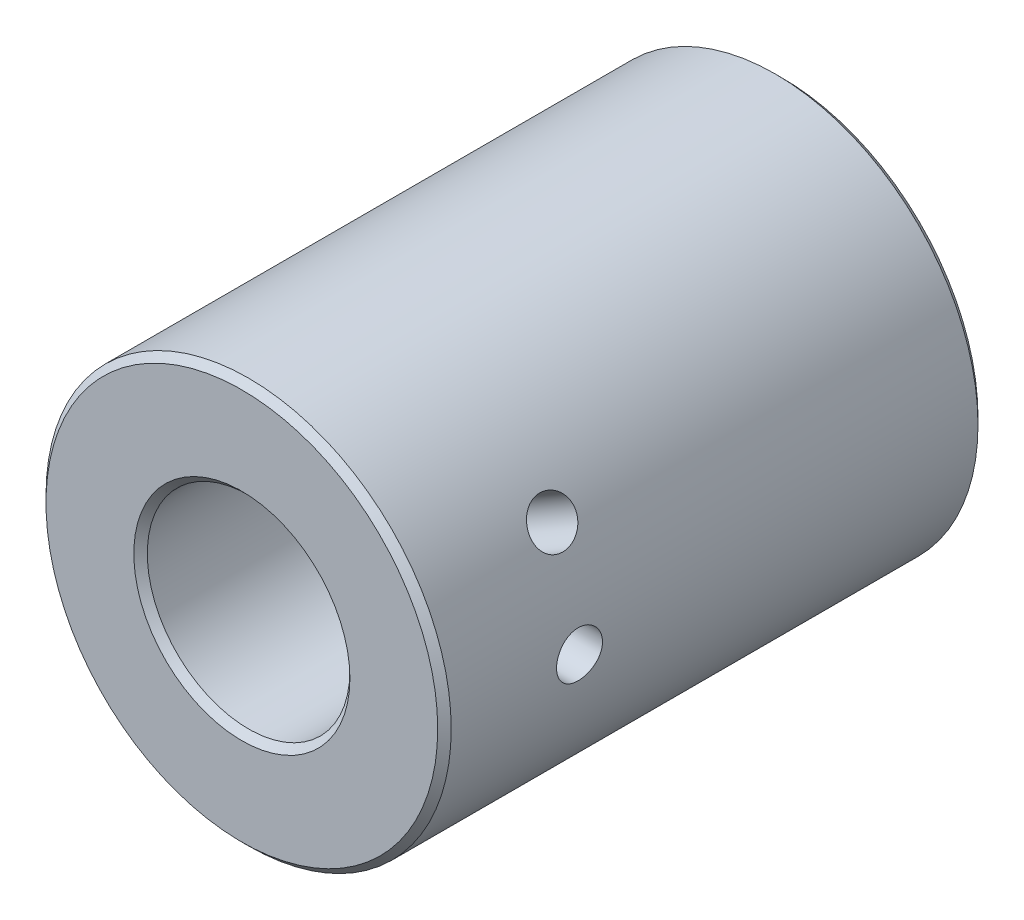
SolidWorks part; units mm, degrees
ref_plane "Přední rovina" through (0, 0, 0) normal (0, 0, 1) x (1, 0, 0)
ref_plane "Horní rovina" through (0, 0, 0) normal (0, 1, 0) x (1, 0, 0)
ref_plane "Pravá rovina" through (0, 0, 0) normal (1, 0, 0) x (0, 0, -1)
sketch "Skica1" plane through (0, 0, 0) normal (0, 0, 1) x (1, 0, 0)
  circle A0 centre (0, 0) radius 30
  circle A1 centre (0, 0) radius 15
  dimension "D1" = 30
  dimension "D2" = 60
extrude "Přidat vysunutím1" add sketch "Skica1" along normal blind 80
chamfer "Zkosení1" distance 1 angle 45 4 edges at (15, 0, 0) (15, 0, 80) (30, 0, 0) (30, 0, 80)
ref_plane "Rovina1" through (0, 0, 0) normal (0.866, 0.5, 0) x (0, 0, -1)
hole_wizard "M8 závit1" positions "3DSkica1" profile "Skica2" tap size "M8" standard "ISO"
sketch3d "3DSkica1"
  point P0 (0, -30, 20)
  point P2 (15, -25.9808, 20)
  point P5 (0, 0, 0)
  point P6 (0, 0, 0)
  dimension "D1" = 20
  dimension "D2" = 20
sketch "Skica2" plane through (0, -30, 20) normal (1, 0, 0) x (0, 0, -1)
  line L0 (0, 0) -> (0, 15)
  line L1 (0, 15) -> (3.4, 15)
  line L2 (3.4, 15) -> (3.4, 0)
  line L5 (3.4, 0) -> (0, 0)
  line L11 (0, -6.35) -> (0, 107.95) construction
  dimension "Průměr závitníku" = 6.8
  dimension "Hloubka závitníku" = 15
cosmetic thread "Závit díry3" parameters "D2"=8
cosmetic thread "Závit díry4" parameters "D2"=8
ref_plane "Rovina2" through (30, 0, 0) normal (1, 0, 0) x (0, 0, -1)
hole_wizard "M8 závit2" positions "Skica3" profile "Skica4" tap size "M8" standard "ISO"
sketch "Skica3" plane through (30, 0, 0) normal (1, 0, 0) x (0, 0, -1)
  line L0 (-79, 0) -> (-1, 0) construction
  line L2 (-80, 29) -> (-80, -29) construction
  point P0 (-60, 0)
  dimension "D1" = 20
sketch "Skica4" plane through (30, 0, 60) normal (0, 1, 0) x (0, 0, -1)
  line L0 (0, 0) -> (0, 60)
  line L1 (0, 60) -> (3.4, 60)
  line L2 (3.4, 60) -> (3.4, 0)
  line L5 (3.4, 0) -> (0, 0)
  line L11 (0, -6.35) -> (0, 107.95) construction
  dimension "Průměr závitníku" = 6.8
  dimension "Hloubka závitníku" = 60
cosmetic thread "Závit díry5" parameters "D2"=8
pattern_circular "Kruhové pole1" count 2 every 30 about axis through (0, 0, 80) along (0, 0, -1) of "M8 závit2"
